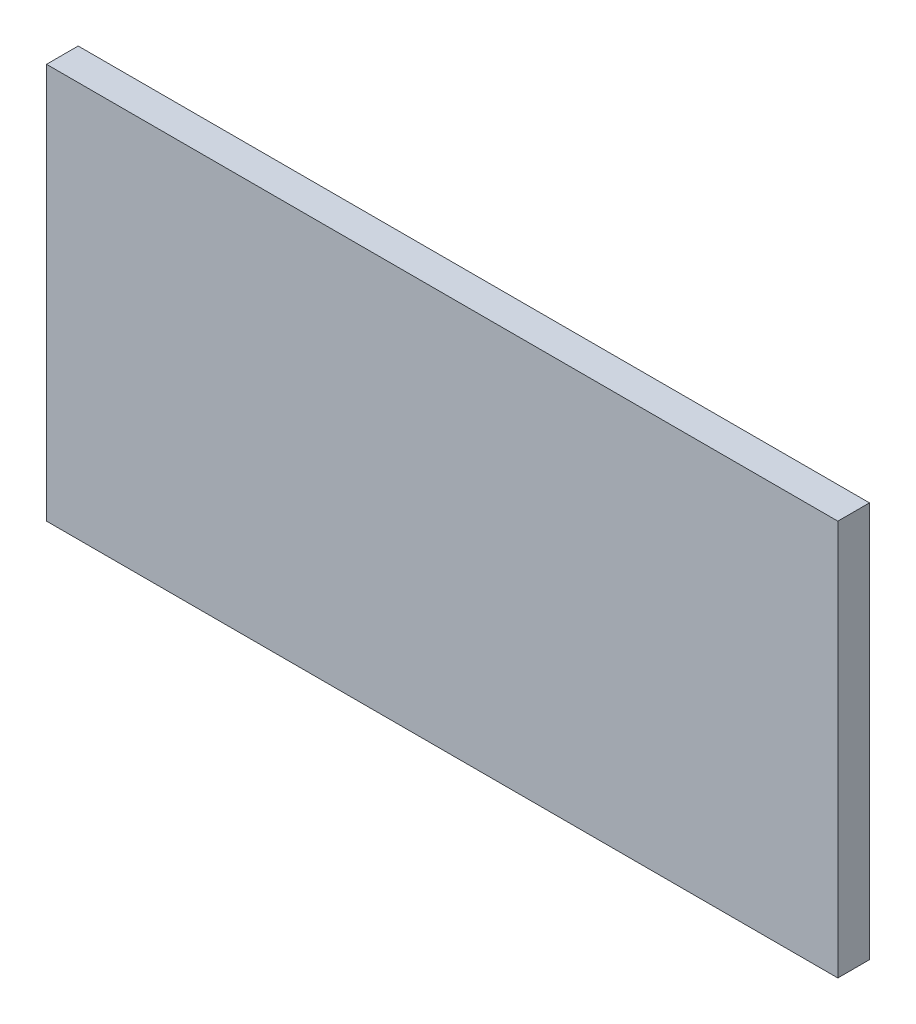
SolidWorks part; units mm, degrees
ref_plane "Front Plane" through (0, 0, 0) normal (0, 0, 1) x (1, 0, 0)
ref_plane "Top Plane" through (0, 0, 0) normal (0, 1, 0) x (1, 0, 0)
ref_plane "Right Plane" through (0, 0, 0) normal (1, 0, 0) x (0, 0, -1)
sketch "Sketch1" plane through (0, 0, 0) normal (0, 0, 1) x (1, 0, 0)
  line L1 (-250, -125) -> (250, -125)
  line L2 (-250, -125) -> (-250, 125)
  line L3 (-250, 125) -> (250, 125)
  line L4 (250, -125) -> (250, 125)
  line L5 (-250, -125) -> (250, 125) construction
  line L6 (-250, 125) -> (250, -125) construction
  point P0 (0, 0)
  dimension "D1" = 250
  dimension "D2" = 500
extrude "Boss-Extrude1" add sketch "Sketch1" along normal blind 20
